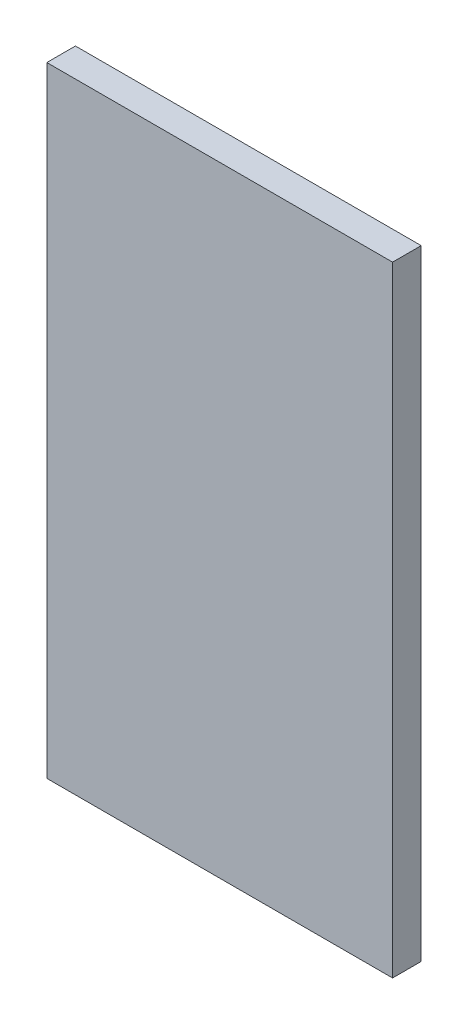
SolidWorks part; units mm, degrees
material "ABS PC"
ref_plane "Front Plane" through (0, 0, 0) normal (0, 0, 1) x (1, 0, 0)
ref_plane "Top Plane" through (0, 0, 0) normal (0, 1, 0) x (1, 0, 0)
ref_plane "Right Plane" through (0, 0, 0) normal (1, 0, 0) x (0, 0, -1)
sketch "Sketch1" plane through (0, 0, 0) normal (0, 0, 1) x (1, 0, 0)
  line L0 (-9.8119, 33.3697) -> (-19.5274, 33.3697) construction
  line L1 (-9.8119, 50.3877) -> (-9.8119, 33.3697) construction
  line L2 (-19.5274, 33.3697) -> (-19.5274, 50.3877) construction
  line L3 (-19.5274, 50.3877) -> (-9.8119, 50.3877) construction
  line L13 (-10.0659, 50.1337) -> (-19.2734, 50.1337)
  line L14 (-10.0659, 33.6237) -> (-10.0659, 50.1337)
  line L15 (-19.2734, 33.6237) -> (-10.0659, 33.6237)
  line L16 (-19.2734, 50.1337) -> (-19.2734, 33.6237)
  dimension "D1" = 0.254
  dimension "D2" = 0.254
  dimension "D3" = 0.254
  dimension "D4" = 0.254
extrude "Boss-Extrude1" add sketch "Sketch1" along normal blind 0.762
